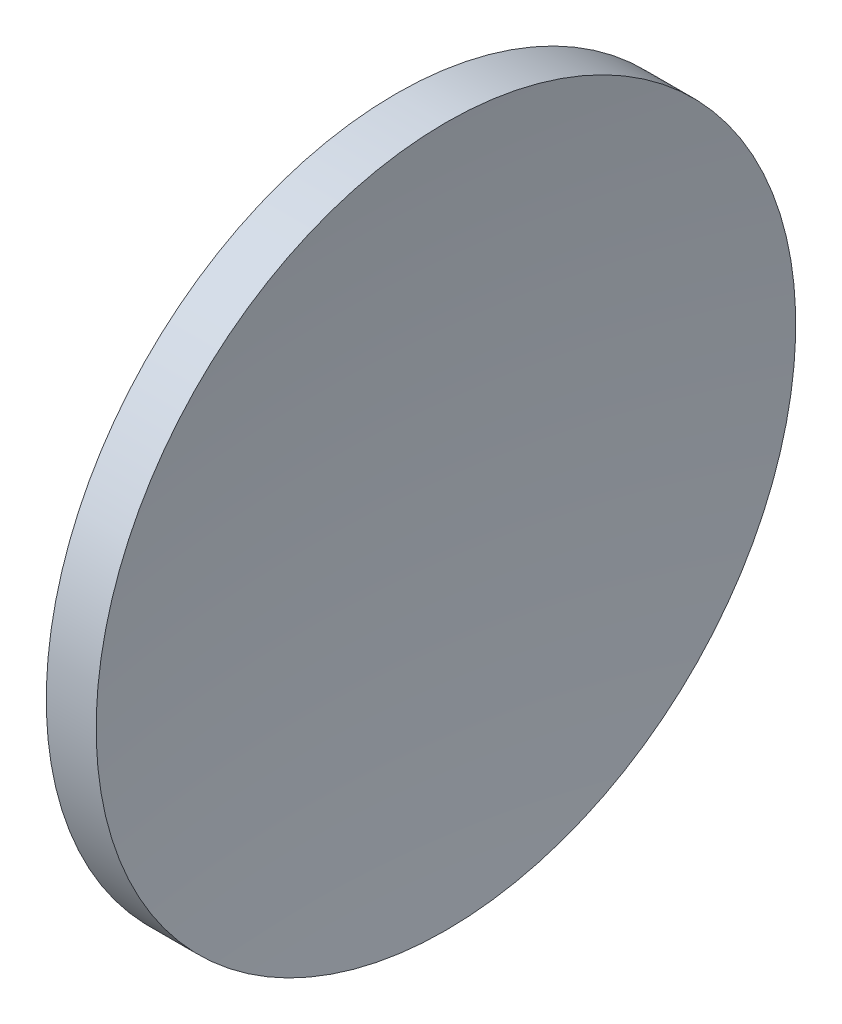
SolidWorks part; units mm, degrees
ref_plane "前视基准面" through (0, 0, 0) normal (0, 0, 1) x (1, 0, 0)
ref_plane "上视基准面" through (0, 0, 0) normal (0, 1, 0) x (1, 0, 0)
ref_plane "右视基准面" through (0, 0, 0) normal (1, 0, 0) x (0, 0, -1)
sketch "草图1" plane through (0, 0, 0) normal (0, 0, 1) x (1, 0, 0)
  line L0 (231.889, 130.4337) -> (271.8964, 130.4337) construction
  line L1 (249.9414, 155.4337) -> (253.5065, 155.4337)
  line L2 (245.2821, 130.4337) -> (251.8821, 130.4337)
  arc A0 (249.9414, 155.4337) -> (245.2821, 130.4337) centre (314.6821, 130.4337) ccw
  arc A1 (253.5065, 155.4337) -> (251.8821, 130.4337) centre (445.0821, 130.4337) ccw
revolve "旋转1" add sketch "草图1" angle 360 about L0
